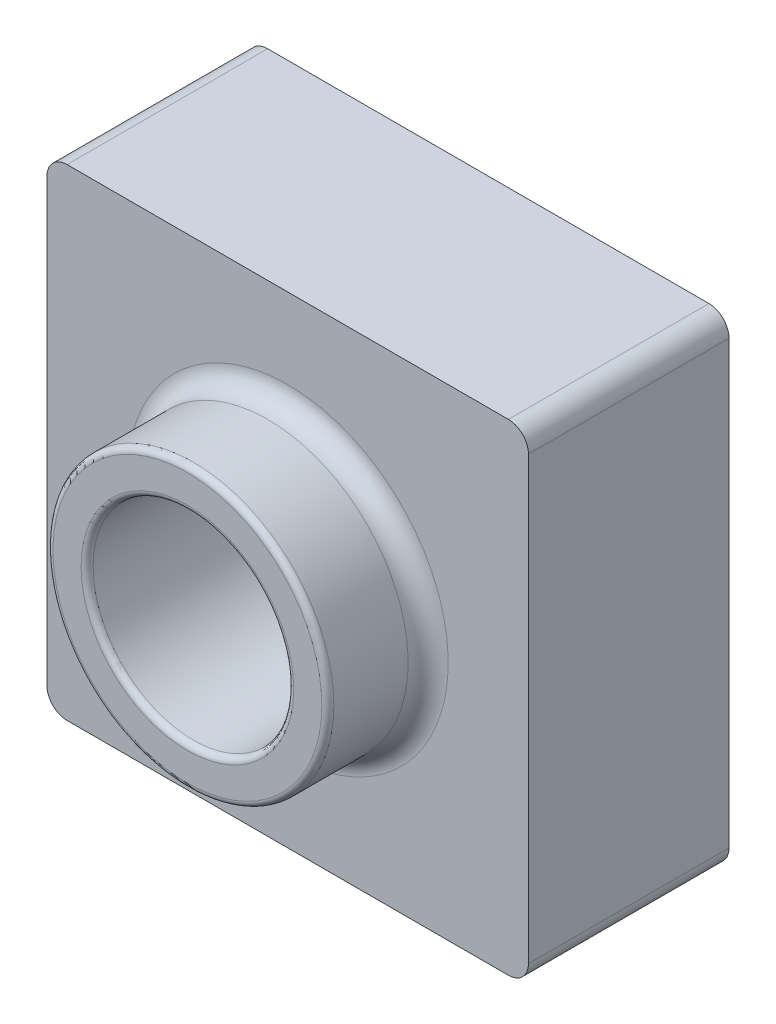
SolidWorks part; units mm, degrees
ref_plane "Front Plane" through (0, 0, 0) normal (0, 0, 1) x (1, 0, 0)
ref_plane "Top Plane" through (0, 0, 0) normal (0, 1, 0) x (1, 0, 0)
ref_plane "Right Plane" through (0, 0, 0) normal (1, 0, 0) x (0, 0, -1)
sketch "Sketch1" plane through (0, 0, 0) normal (0, 0, 1) x (1, 0, 0)
  line L1 (0, 0) -> (3048, 0)
  line L2 (0, 0) -> (0, 3048)
  line L3 (0, 3048) -> (3048, 3048)
  line L4 (3048, 0) -> (3048, 3048)
  dimension "D1" = 3048
  dimension "D2" = 3048
extrude "Boss-Extrude1" add sketch "Sketch1" against normal blind 1270 contours L3 L4 L1 L2
sketch "Sketch3" plane through (0, 0, 0) normal (0, 0, 1) x (1, 0, 0)
  circle A0 centre (1524, 1524) radius 889
  dimension "D1" = 1778
  dimension "D2" = 1524
  dimension "D3" = 1524
extrude "Boss-Extrude2" add sketch "Sketch3" along normal blind 635
sketch "Sketch8" plane through (0, 0, 635) normal (0, 0, 1) x (1, 0, 0)
  circle A0 centre (1524, 1524) radius 635
  dimension "D1" = 1270
extrude "Cut-Extrude1" cut sketch "Sketch8" against normal through all contours A0
fillet "Fillet11" radius 127 1 edges at (635, 1524, 0)
fillet "Fillet12" radius 38.1 2 edges at (2159, 1524, 635) (2413, 1524, 635)
shell "Shell1" thickness 50.8
fillet "Fillet13" radius 127 4 edges at (3048, 3048, -635) (3048, 0, -635) (0, 0, -635) (0, 3048, -635)
